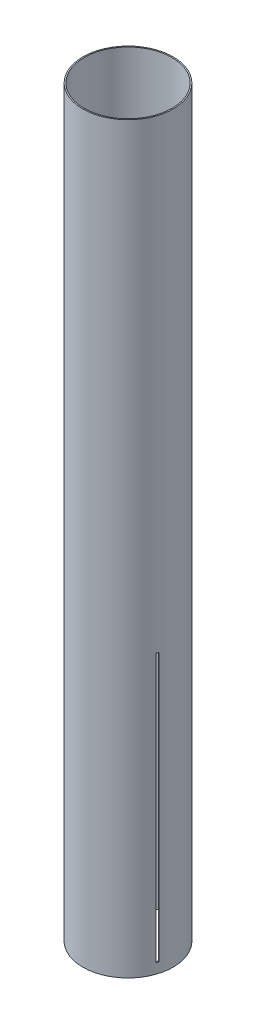
SolidWorks part; units mm, degrees
ref_plane "Front Plane" through (0, 0, 0) normal (0, 0, 1) x (1, 0, 0)
ref_plane "Top Plane" through (0, 0, 0) normal (0, 1, 0) x (1, 0, 0)
ref_plane "Right Plane" through (0, 0, 0) normal (1, 0, 0) x (0, 0, -1)
sketch "Sketch2" plane through (0, 0, 0) normal (0, 1, 0) x (1, 0, 0)
  circle A0 centre (0, 0) radius 49.5808
  circle A1 centre (0, 0) radius 50.9524
  dimension "D1" = 99.1616
  dimension "D2" = 101.9048
extrude "Boss-Extrude1" add sketch "Sketch2" along normal blind 838.2
sketch "Sketch3" plane through (0, 0, 0) normal (0, 0, 1) x (1, 0, 0)
  line L0 (-50.9524, 0) -> (50.9524, 0) construction
  line L1 (-12.5257, 11.3538) -> (-9.5285, 11.3538)
  line L2 (-12.5257, 11.3538) -> (-12.5257, 313.6138)
  line L3 (-12.5257, 313.6138) -> (-9.5285, 313.6138)
  line L4 (-9.5285, 11.3538) -> (-9.5285, 313.6138)
  point P4 (0, 0)
  dimension "D1" = 2.9972
  dimension "D2" = 302.26
  dimension "D3" = 11.3538
extrude "Cut-Extrude1" cut sketch "Sketch3" against normal through all contours L1 L4 L3 L2
pattern_circular "CirPattern2" count 3 over 360 about axis through (0, 0, 0) along (0, 1, 0) of "Cut-Extrude1"
